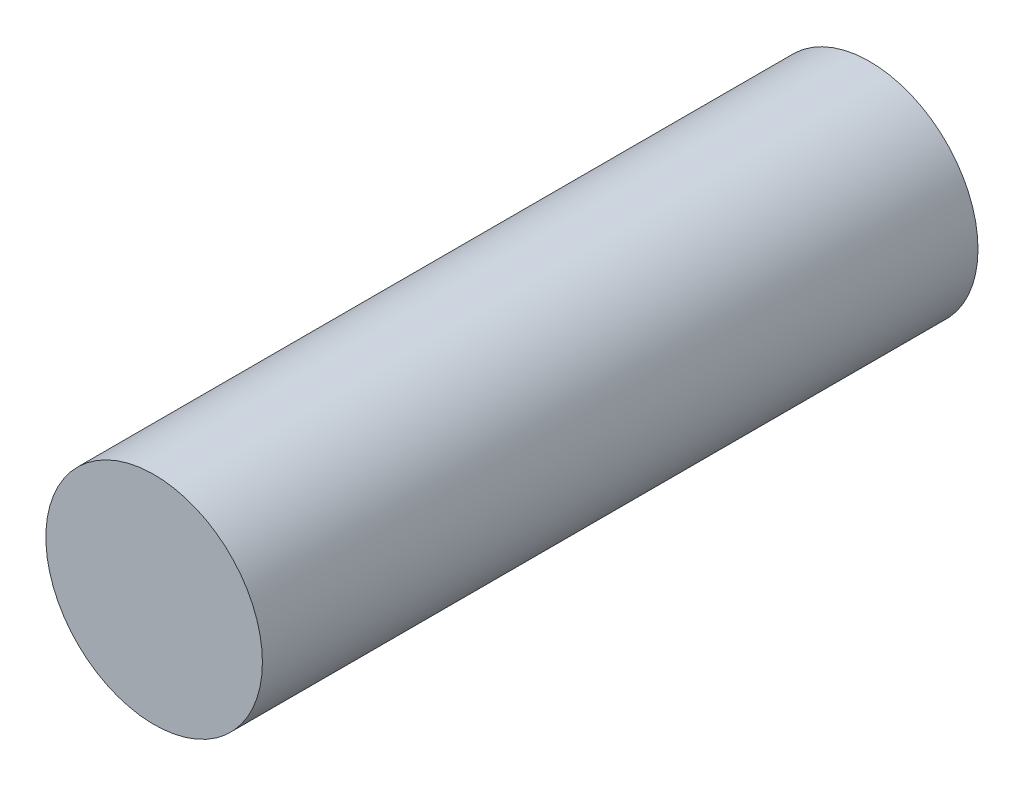
SolidWorks part; units mm, degrees
material "6061-T6 (SS)"
ref_plane "Front Plane" through (0, 0, 0) normal (0, 0, 1) x (1, 0, 0)
ref_plane "Top Plane" through (0, 0, 0) normal (0, 1, 0) x (1, 0, 0)
ref_plane "Right Plane" through (0, 0, 0) normal (1, 0, 0) x (0, 0, -1)
sketch "Sketch1" plane through (0, 0, 0) normal (0, 0, 1) x (1, 0, 0)
  circle A0 centre (0, 0) radius 18.2563
  dimension "D1" = 36.5125
extrude "Boss-Extrude1" add sketch "Sketch1" along normal mid plane 120.65
chamfer "Chamfer1" [suppressed] distance 25.4 distance2 3.9688
